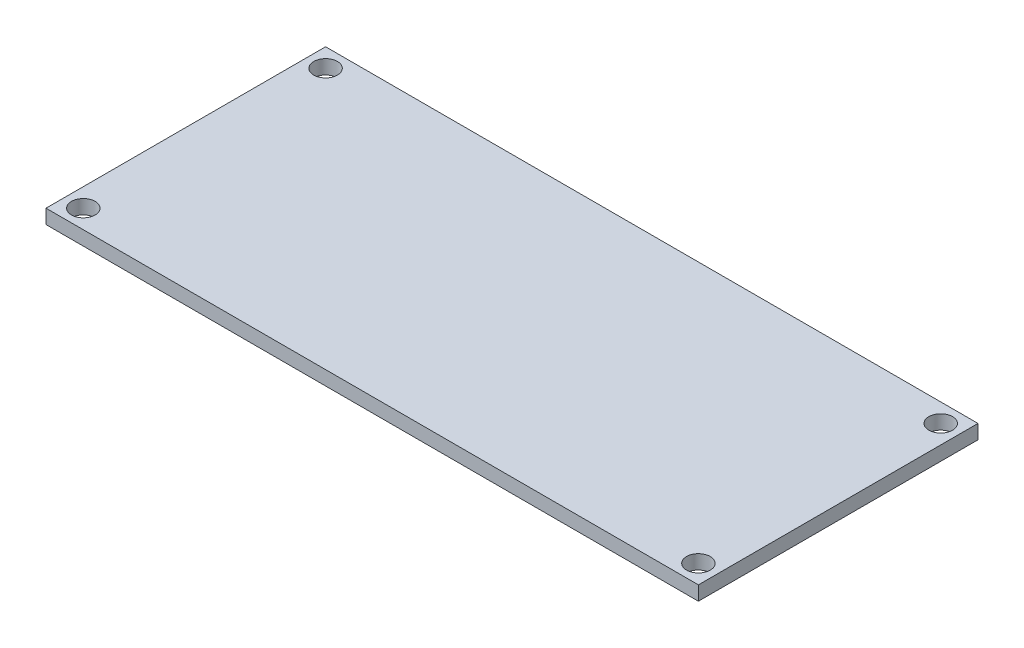
SolidWorks part; units mm, degrees
ref_plane "Front Plane" through (0, 0, 0) normal (0, 0, 1) x (1, 0, 0)
ref_plane "Top Plane" through (0, 0, 0) normal (0, 1, 0) x (1, 0, 0)
ref_plane "Right Plane" through (0, 0, 0) normal (1, 0, 0) x (0, 0, -1)
sketch "Sketch1" plane through (0, 0, 0) normal (0, 1, 0) x (1, 0, 0)
  line L1 (-29.4524, 16.3095) -> (40.5476, 16.3095)
  line L2 (-29.4524, 16.3095) -> (-29.4524, -13.6905)
  line L3 (-29.4524, -13.6905) -> (40.5476, -13.6905)
  line L4 (40.5476, 16.3095) -> (40.5476, -13.6905)
  dimension "D1" = 30
  dimension "D2" = 70
extrude "Boss-Extrude1" add sketch "Sketch1" along normal blind 1.524
sketch "Sketch2" plane through (0, 1.524, 0) normal (0, 1, 0) x (1, 0, 0)
  line L0 (-29.4524, -13.6905) -> (40.5476, -13.6905) construction
  line L1 (-29.4524, 16.3095) -> (-29.4524, -13.6905) construction
  circle A0 centre (-27.4524, -11.6905) radius 1.27
  dimension "D1" = 2
  dimension "D2" = 2
extrude "Cut-Extrude1" cut sketch "Sketch2" against normal through all
ref_plane "Plane1" through (5.5476, 0, 0) normal (-1, 0, 0) x (0, 0, 1)
ref_plane "Plane2" through (0, 0, -1.3095) normal (0, 0, -1) x (-1, 0, 0)
mirror "Mirror1" about plane through (5.5476, 0, 0) normal (-1, 0, 0) of "Cut-Extrude1"
mirror "Mirror2" about plane through (0, 0, -1.3095) normal (0, 0, -1) of "Mirror1", "Cut-Extrude1"
